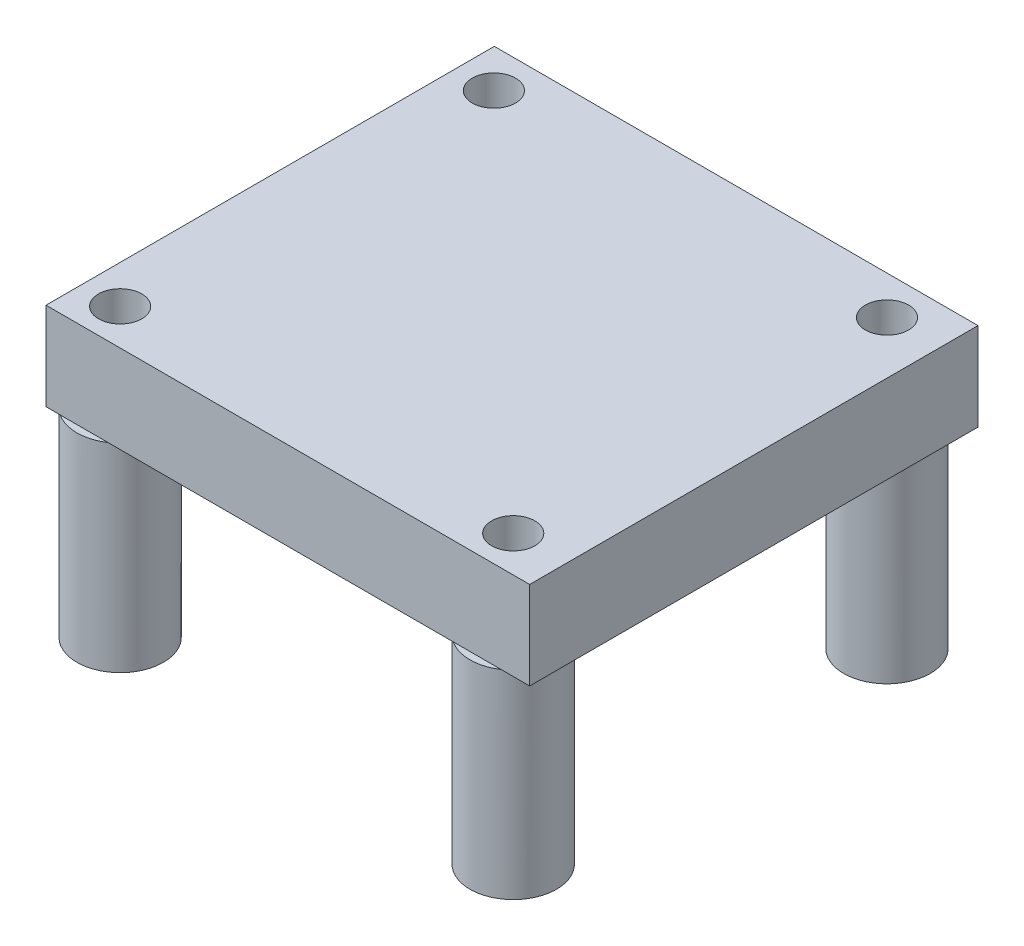
SolidWorks part; units mm, degrees
ref_plane "Front Plane" through (0, 0, 0) normal (0, 0, 1) x (1, 0, 0)
ref_plane "Top Plane" through (0, 0, 0) normal (0, 1, 0) x (1, 0, 0)
ref_plane "Right Plane" through (0, 0, 0) normal (1, 0, 0) x (0, 0, -1)
sketch "Sketch1" plane through (0, 0, 0) normal (0, 1, 0) x (1, 0, 0)
  line L1 (-11.2829, 10.6292) -> (16.6571, 10.6292)
  line L2 (-11.2829, 10.6292) -> (-11.2829, -15.2708)
  line L3 (-11.2829, -15.2708) -> (16.6571, -15.2708)
  line L4 (16.6571, 10.6292) -> (16.6571, -15.2708)
  dimension "D1" = 27.94
  dimension "D2" = 25.9
extrude "Boss-Extrude1" add sketch "Sketch1" along normal blind 5.08
sketch "Sketch2" plane through (0, 0, 0) normal (0, -1, 0) x (1, 0, 0)
  circle A0 centre (-9.0827, 13.1869) radius 2.5
  circle A1 centre (13.6249, 13.1869) radius 2.5
  circle A2 centre (-9.0827, -8.4031) radius 2.5
  circle A3 centre (13.6249, -8.4031) radius 2.5
  circle A4 centre (-9.0827, 13.1869) radius 1.25
  circle A5 centre (-9.0827, -8.4031) radius 1.25
  circle A6 centre (13.6249, 13.1869) radius 1.25
  circle A7 centre (13.6249, -8.4031) radius 1.25
  dimension "D1" = 5
  dimension "D2" = 2.5
  dimension "D3" = 2.5
  dimension "D4" = 5
  dimension "D5" = 2.5
  dimension "D6" = 5
  dimension "D7" = 2.5
  dimension "D8" = 5
  dimension "D9" = 21.59
  dimension "D10" = 22.7076
extrude "Boss-Extrude2" add sketch "Sketch2" along normal blind 11.4808
sketch "Sketch3" plane through (0, 5.08, 0) normal (0, 1, 0) x (1, 0, 0)
  circle A0 centre (13.6249, 8.4031) radius 1.25
  circle A1 centre (-9.0827, 8.4031) radius 1.25
  circle A2 centre (13.6249, -13.1869) radius 1.25
  circle A3 centre (-9.0827, -13.1869) radius 1.25
  dimension "D1" = 2.5
  dimension "D2" = 2.5
  dimension "D3" = 2.5
  dimension "D4" = 2.5
extrude "Cut-Extrude1" cut sketch "Sketch3" against normal through all both
